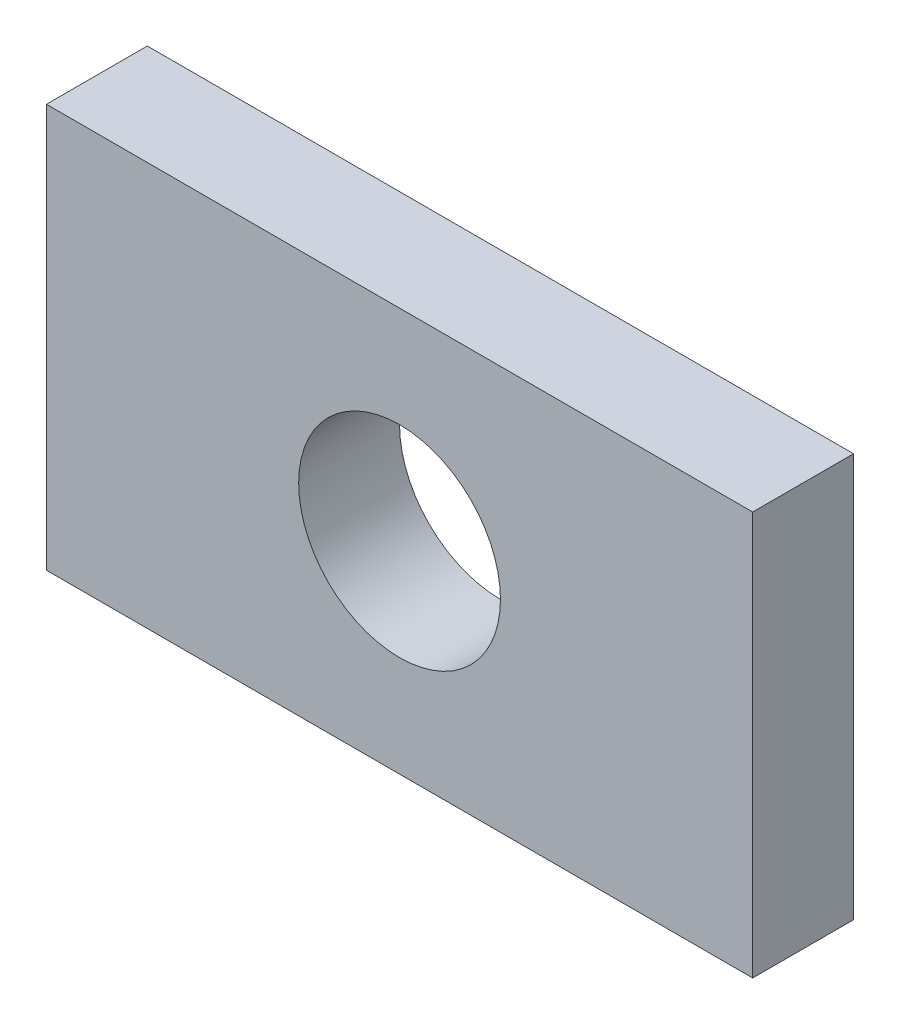
SolidWorks part; units mm, degrees
ref_plane "Front Plane" through (0, 0, 0) normal (0, 0, 1) x (1, 0, 0)
ref_plane "Top Plane" through (0, 0, 0) normal (0, 1, 0) x (1, 0, 0)
ref_plane "Right Plane" through (0, 0, 0) normal (1, 0, 0) x (0, 0, -1)
sketch "Sketch1" plane through (0, 0, 0) normal (0, 0, 1) x (1, 0, 0)
  line L1 (0, 0) -> (17.78, 0)
  line L2 (0, 0) -> (0, 10.16)
  line L3 (0, 10.16) -> (17.78, 10.16)
  line L4 (17.78, 0) -> (17.78, 10.16)
  circle A0 centre (8.89, 5.08) radius 2.54
  dimension "D3" = 5.08
  dimension "D4" = 5.08
  dimension "D1" = 17.78
  dimension "D2" = 10.16
  dimension "D5" = 8.89
extrude "Boss-Extrude1" add sketch "Sketch1" along normal blind 2.54
